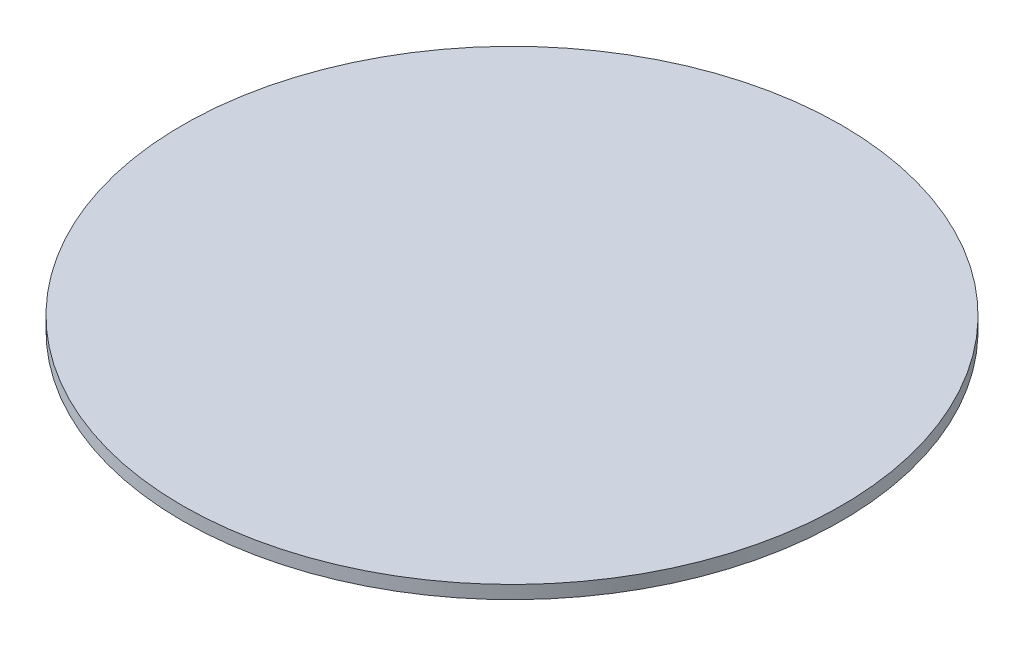
SolidWorks part; units mm, degrees
ref_plane "Front Plane" through (0, 0, 0) normal (0, 0, 1) x (1, 0, 0)
ref_plane "Top Plane" through (0, 0, 0) normal (0, 1, 0) x (1, 0, 0)
ref_plane "Right Plane" through (0, 0, 0) normal (1, 0, 0) x (0, 0, -1)
sketch "Sketch1" plane through (0, 0, 0) normal (0, 1, 0) x (1, 0, 0)
  circle A0 centre (0, 0) radius 20
extrude "Boss-Extrude1" add sketch "Sketch1" along normal blind 0.8
